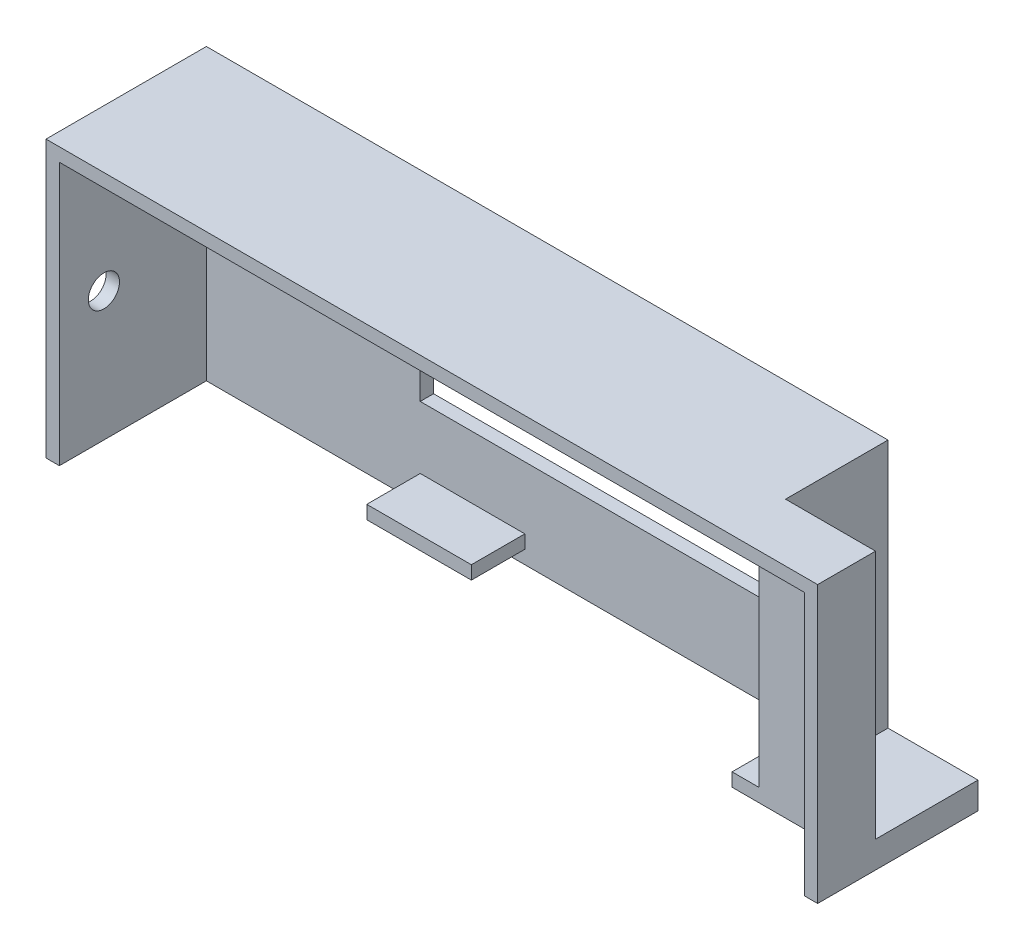
SolidWorks part; units mm, degrees
ref_plane "Front Plane" through (0, 0, 0) normal (0, 0, 1) x (1, 0, 0)
ref_plane "Top Plane" through (0, 0, 0) normal (0, 1, 0) x (1, 0, 0)
ref_plane "Right Plane" through (0, 0, 0) normal (1, 0, 0) x (0, 0, -1)
sketch "Sketch1" plane through (0, 0, 0) normal (0, 1, 0) x (1, 0, 0)
  line L1 (-43.3, 9) -> (43.3, 9)
  line L2 (-43.3, 9) -> (-43.3, -9)
  line L3 (-43.3, -9) -> (43.3, -9)
  line L4 (43.3, 9) -> (43.3, -9)
  line L5 (-43.3, 9) -> (43.3, -9) construction
  line L6 (-43.3, -9) -> (43.3, 9) construction
  point P0 (0, 0)
  dimension "D1" = 86.6
  dimension "D2" = 18
extrude "Boss-Extrude1" add sketch "Sketch1" along normal blind 31
sketch "Sketch7" plane through (0, 31, 0) normal (0, 1, 0) x (1, 0, 0)
  line L0 (-43.3, 9) -> (-43.3, -9) construction
  line L1 (43.3, 9) -> (33.2, 9)
  line L2 (43.3, 9) -> (43.3, -2.5)
  line L3 (43.3, -2.5) -> (33.2, -2.5)
  line L4 (33.2, 9) -> (33.2, -2.5)
  dimension "D1" = 11.5
  dimension "D2" = 76.5
extrude "Cut-Extrude1" cut sketch "Sketch7" against normal blind 28
shell "Shell1" thickness 1.5
sketch "Sketch10" plane through (0, 1.5, 0) normal (0, 1, 0) x (1, 0, 0)
  line L0 (-41.8, 7.5) -> (31.7, 7.5)
  line L1 (31.7, 7.5) -> (31.7, -4)
  line L2 (31.7, -4) -> (41.8, -4)
  line L3 (41.8, -4) -> (41.8, -9)
  line L4 (41.8, -9) -> (-41.8, -9)
  line L5 (-41.8, -9) -> (-41.8, 7.5)
extrude "Cut-Extrude2" cut sketch "Sketch10" against normal through all
sketch "Sketch11" plane through (0, 0, 0) normal (0, -1, 0) x (1, 0, 0)
  line L0 (41.8, 4) -> (31.7, 4)
  line L1 (31.7, 4) -> (31.7, -7.5)
  line L2 (31.7, -7.5) -> (41.8, -7.5)
  line L3 (41.8, -7.5) -> (41.8, 4)
extrude "Cut-Extrude3" cut sketch "Sketch11" against normal offset from surface (1.5 mm away) 1.5
sketch "Sketch12" plane through (0, 3, 0) normal (0, 1, 0) x (1, 0, 0)
  line L0 (-43.3, 9) -> (-43.3, -9) construction
  line L1 (43.3, 9) -> (33.2, 9) construction
  circle A0 centre (35.2, 0.5) radius 2
  dimension "D1" = 4
  dimension "D2" = 78.5
  dimension "D3" = 8.5
extrude "Cut-Extrude4" cut sketch "Sketch12" against normal through all both and the other way through all
sketch "Sketch14" plane through (-43.3, 0, 0) normal (-1, 0, 0) x (0, 0, 1)
  line L0 (-9, 31) -> (-9, 0) construction
  line L1 (-9, 31) -> (9, 31) construction
  circle A0 centre (4, 14.5) radius 1.75
  dimension "D1" = 3.5
  dimension "D2" = 13
  dimension "D3" = 16.5
extrude "Cut-Extrude6" cut sketch "Sketch14" against normal up to next
sketch "Sketch15" plane through (-43.3, 0, 0) normal (-1, 0, 0) x (0, 0, 1)
  line L0 (-9, 31) -> (-9, 0) construction
  line L1 (-9, 31) -> (9, 31) construction
  circle A0 centre (0.5, 26) radius 2.25
  point P6 (0, 0)
  dimension "D1" = 4.5
  dimension "D2" = 9.5
  dimension "D3" = 5
extrude "Cut-Extrude7" cut sketch "Sketch15" against normal up to next
sketch "Sketch16" plane through (31.7, 0, 0) normal (-1, 0, 0) x (0, 0, 1)
  line L0 (-7.5, 1.5) -> (-7.5, 29.5) construction
  line L1 (4, 1.5) -> (-7.5, 1.5)
  line L2 (4, 1.5) -> (4, 3)
  line L3 (4, 3) -> (-7.5, 3)
  line L4 (-7.5, 1.5) -> (-7.5, 3)
  dimension "D1" = 1.5
extrude "Boss-Extrude6" add sketch "Sketch16" along normal blind 3
sketch "Sketch17" plane through (0, 0, -9) normal (0, 0, -1) x (-1, 0, 0)
  line L0 (-43.3, 0) -> (43.3, 0) construction
  line L1 (17.8, 0) -> (-28.2, 0)
  line L2 (17.8, 0) -> (17.8, 17.5)
  line L3 (17.8, 17.5) -> (-28.2, 17.5)
  line L4 (-28.2, 0) -> (-28.2, 17.5)
  line L5 (43.3, 31) -> (43.3, 0) construction
  line L6 (-33.2, 31) -> (43.3, 31) construction
  dimension "D1" = 25.5
  dimension "D2" = 71.5
  dimension "D3" = 13.5
extrude "Cut-Extrude8" cut sketch "Sketch17" against normal up to next
sketch "Sketch18" plane through (0, 0, -7.5) normal (0, 0, 1) x (1, 0, 0)
  line L0 (28.2, 17.5) -> (28.2, 0) construction
  line L1 (-17.8, 0) -> (28.2, 0)
  line L2 (-17.8, 0) -> (-17.8, 10)
  line L3 (-17.8, 10) -> (28.2, 10)
  line L4 (28.2, 0) -> (28.2, 10)
  dimension "D1" = 10
extrude "Boss-Extrude7" add sketch "Sketch18" against normal up to surface (1.5 mm away)
sketch "Sketch20" plane through (0, 0, -7.5) normal (0, 0, 1) x (1, 0, 0)
  line L0 (-17.8, 10) -> (-17.8, 17.5) construction
  line L1 (-17.8, 3) -> (-6.0596, 3)
  line L2 (-17.8, 3) -> (-17.8, 1.5)
  line L3 (-17.8, 1.5) -> (-6.0596, 1.5)
  line L4 (-6.0596, 3) -> (-6.0596, 1.5)
  line L5 (28.7, 3) -> (31.7, 3) construction
  dimension "D1" = 1.5
  dimension "D2" = 0
  dimension "D3" = 0
extrude "Boss-Extrude8" add sketch "Sketch20" along normal blind 6
equation "\"1.5.00mm\"=28"
